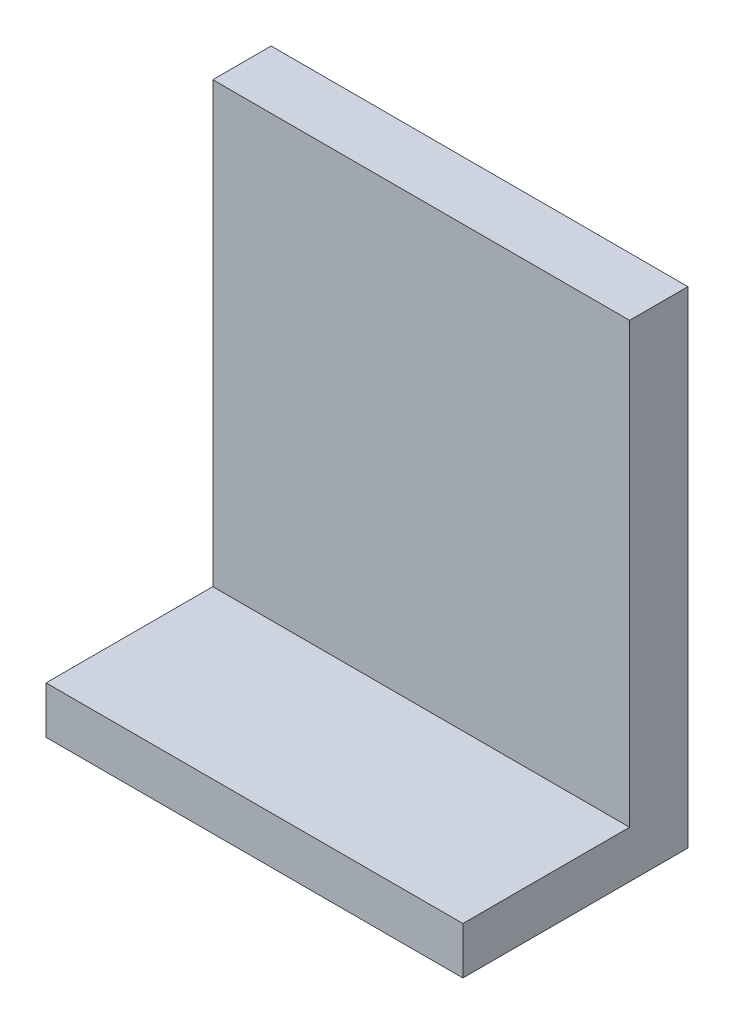
SolidWorks part; units mm, degrees
ref_plane "Front Plane" through (0, 0, 0) normal (0, 0, 1) x (1, 0, 0)
ref_plane "Top Plane" through (0, 0, 0) normal (0, 1, 0) x (1, 0, 0)
ref_plane "Right Plane" through (0, 0, 0) normal (1, 0, 0) x (0, 0, -1)
sketch "Sketch2" plane through (0, 0, 0) normal (0, 0, 1) x (1, 0, 0)
  line L1 (0, 0) -> (50, 0)
  line L2 (0, 0) -> (0, -58.3196)
  line L3 (0, -58.3196) -> (50, -58.3196)
  line L4 (50, 0) -> (50, -58.3196)
  line L5 (0, 0) -> (50, -58.3196) construction
  line L6 (0, -58.3196) -> (50, 0) construction
  point P4 (25, -29.1598)
  dimension "D1" = 50
  dimension "D2" = 58.3196
extrude "Boss-Extrude1" add sketch "Sketch2" along normal blind 7
sketch "Sketch3" plane through (0, 0, 7) normal (0, 0, 1) x (1, 0, 0)
  line L0 (0, 0) -> (0, -58.3196) construction
  line L1 (0, -52.6612) -> (50, -52.6612)
  line L2 (0, -52.6612) -> (0, -58.3196)
  line L3 (0, -58.3196) -> (50, -58.3196)
  line L4 (50, -52.6612) -> (50, -58.3196)
  line L5 (0, -52.6612) -> (50, -58.3196) construction
  line L6 (0, -58.3196) -> (50, -52.6612) construction
  point P4 (25, -55.4904)
extrude "Boss-Extrude2" add sketch "Sketch3" along normal blind 20
